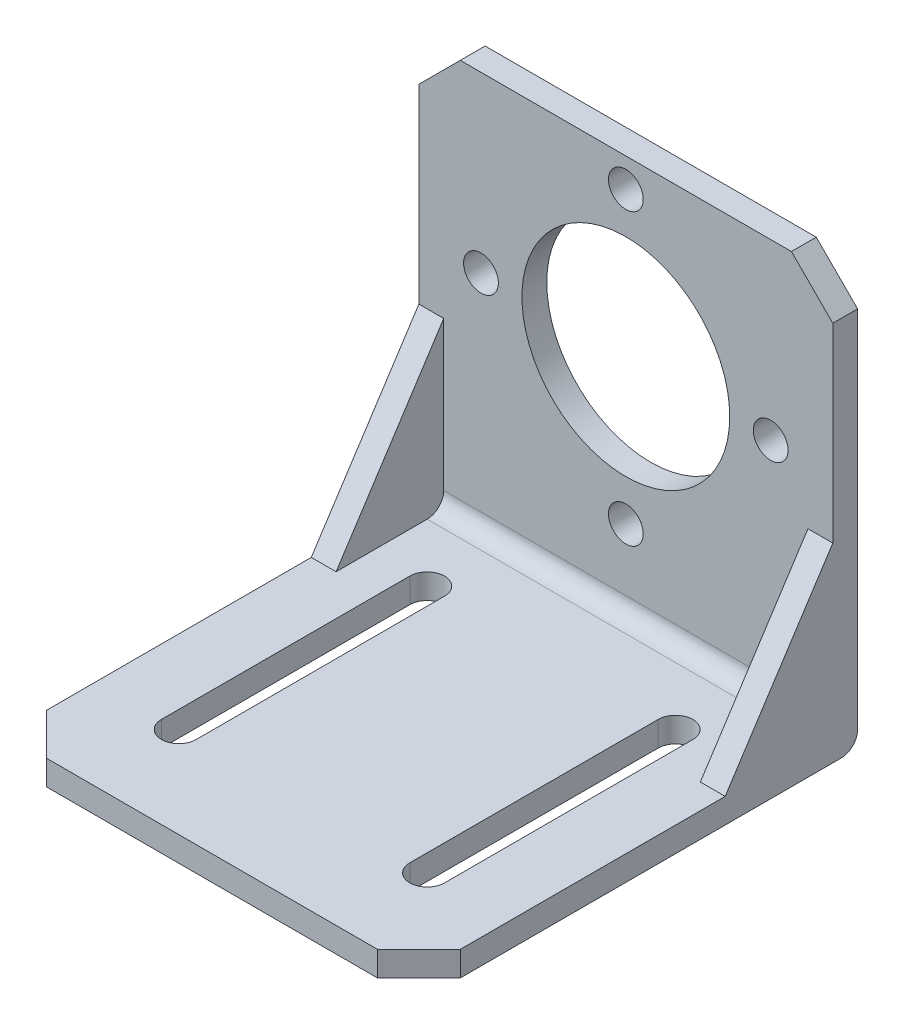
SolidWorks part; units mm, degrees
material "Ст 3 ГОСТ 380-88"
ref_plane "Front Plane" through (0, 0, 0) normal (0, 0, 1) x (1, 0, 0)
ref_plane "Top Plane" through (0, 0, 0) normal (0, 1, 0) x (1, 0, 0)
ref_plane "Right Plane" through (0, 0, 0) normal (1, 0, 0) x (0, 0, -1)
sketch "Sketch1" plane through (0, 0, 0) normal (0, 0, 1) x (1, 0, 0)
  line L1 (-25, -25.5) -> (25, -25.5)
  line L2 (-25, -25.5) -> (-25, 25.5)
  line L3 (-25, 25.5) -> (25, 25.5)
  line L4 (25, -25.5) -> (25, 25.5)
  line L5 (-25, -25.5) -> (25, 25.5) construction
  line L6 (-25, 25.5) -> (25, -25.5) construction
  point P0 (0, 0)
  dimension "D1" = 50
  dimension "D2" = 51
extrude "Boss-Extrude1" add sketch "Sketch1" along normal blind 3
sketch "Sketch2" plane through (0, 0, 3) normal (0, 0, 1) x (1, 0, 0)
  line L0 (25, -25.5) -> (25, 25.5) construction
  line L1 (-25, -25.5) -> (25, -25.5)
  line L2 (-25, -25.5) -> (-25, -22.5)
  line L3 (-25, -22.5) -> (25, -22.5)
  line L4 (25, -25.5) -> (25, -22.5)
  dimension "D1" = 3
extrude "Boss-Extrude2" add sketch "Sketch2" along normal blind 50
fillet "Fillet1" radius 2 2 edges at (0, -25.5, 0) (0, -22.5, 3)
chamfer "Chamfer1" distance 5 angle 45 4 edges at (-25, -24, 53) (25, -24, 53) (25, 25.5, 1.5) (-25, 25.5, 1.5)
sketch "Sketch3" plane through (0, -22.5, 0) normal (0, 1, 0) x (1, 0, 0)
  line L0 (-15, -42) -> (-15, -12) construction
  line L1 (-17.1, -42) -> (-17.1, -12)
  line L2 (-12.9, -42) -> (-12.9, -12)
  line L3 (15, -42) -> (15, -12) construction
  line L4 (12.9, -42) -> (12.9, -12)
  line L5 (17.1, -42) -> (17.1, -12)
  line L6 (20, -53) -> (-20, -53) construction
  line L7 (-15, -27) -> (15, -27) construction
  arc A0 (-17.1, -42) -> (-12.9, -42) centre (-15, -42) ccw
  arc A1 (-12.9, -12) -> (-17.1, -12) centre (-15, -12) ccw
  arc A2 (12.9, -42) -> (17.1, -42) centre (15, -42) ccw
  arc A3 (17.1, -12) -> (12.9, -12) centre (15, -12) ccw
  point P2 (-15, -27)
  point P7 (15, -27)
  point P18 (0, -27)
  dimension "D1" = 4.2
  dimension "D2" = 30
  dimension "D3" = 11
  dimension "D4" = 30
extrude "Cut-Extrude1" cut sketch "Sketch3" against normal blind 50
sketch "Sketch4" plane through (0, 0, 3) normal (0, 0, 1) x (1, 0, 0)
  line L0 (20, 25.5) -> (-20, 25.5) construction
  circle A0 centre (0, 4.5) radius 12.55
  circle A1 centre (0, 4.5) radius 17.5 construction
  circle A2 centre (0, 22) radius 2.1
  circle A3 centre (0, -13) radius 2.1
  circle A4 centre (17.5, 4.5) radius 2.1
  circle A5 centre (-17.5, 4.5) radius 2.1
  dimension "D2" = 25.1
  dimension "D3" = 35
  dimension "D4" = 4.2
  dimension "D1" = 21
extrude "Cut-Extrude2" cut sketch "Sketch4" against normal blind 50
sketch "Sketch5" plane through (-25, 0, 0) normal (-1, 0, 0) x (0, 0, 1)
  line L0 (3, -2.5) -> (16, -22.5)
  line L1 (3, 20.5) -> (3, -20.5) construction
  line L2 (48, -22.5) -> (5, -22.5) construction
  line L3 (16, -22.5) -> (5, -22.5)
  line L4 (3, -20.5) -> (3, -2.5)
  arc A0 (5, -22.5) -> (3, -20.5) centre (5, -20.5) cw
  dimension "D1" = 20
  dimension "D2" = 13
extrude "Boss-Extrude3" add sketch "Sketch5" against normal blind 3
mirror "Mirror1" about plane through (0, 0, 0) normal (1, 0, 0) of "Boss-Extrude3"
